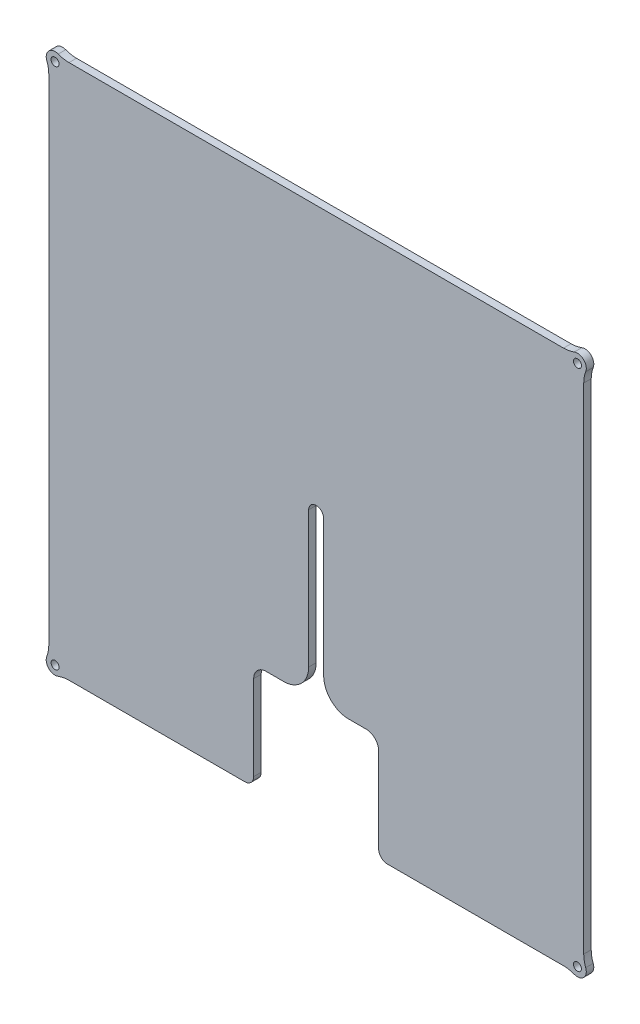
SolidWorks part; units mm, degrees
material "Balsa"
ref_plane "Front Plane" through (0, 0, 0) normal (0, 0, 1) x (1, 0, 0)
ref_plane "Top Plane" through (0, 0, 0) normal (0, 1, 0) x (1, 0, 0)
ref_plane "Right Plane" through (0, 0, 0) normal (1, 0, 0) x (0, 0, -1)
sketch "Sketch1" plane through (0, 0, 0) normal (0, 0, 1) x (1, 0, 0)
  line L0 (-107, 98.923) -> (-107, -98.923)
  line L1 (98.923, 107) -> (-98.923, 107)
  line L2 (107, -98.923) -> (107, 98.923)
  line L3 (43, -107) -> (98.923, -107)
  line L4 (43, -107) -> (43, -101) construction
  line L5 (39, -97) -> (-39, -97) construction
  line L6 (-43, -101) -> (-43, -107) construction
  line L7 (-98.923, -107) -> (-43, -107)
  line L8 (-43, -107) -> (43, -107)
  line L9 (104.5, -104.5) -> (-104.5, -104.5) construction
  line L10 (104.5, -104.5) -> (104.5, 104.5) construction
  line L11 (104.5, 104.5) -> (-104.5, 104.5) construction
  line L12 (-104.5, -104.5) -> (-104.5, 104.5) construction
  line L13 (104.5, -104.5) -> (-104.5, 104.5) construction
  line L14 (104.5, 104.5) -> (-104.5, -104.5) construction
  circle A0 centre (-104.5, -104.5) radius 1.6
  circle A1 centre (-104.5, 104.5) radius 1.6
  circle A2 centre (104.5, 104.5) radius 1.6
  circle A3 centre (104.5, -104.5) radius 1.6
  arc A4 (43, -101) -> (39, -97) centre (39, -101) ccw construction
  arc A5 (-39, -97) -> (-43, -101) centre (-39, -101) ccw construction
  arc A6 (-103.2308, 107.7999) -> (-107.7999, 103.2308) centre (-104.5, 104.5) ccw
  arc A8 (-107.7999, -103.2308) -> (-103.2308, -107.7999) centre (-104.5, -104.5) ccw
  arc A9 (98.923, -107) -> (103.2308, -107.7999) centre (98.923, -119) cw
  arc A10 (103.2308, -107.7999) -> (107.7999, -103.2308) centre (104.5, -104.5) ccw
  arc A13 (107.7999, 103.2308) -> (103.2308, 107.7999) centre (104.5, 104.5) ccw
  arc A14 (107, -98.923) -> (107.7999, -103.2308) centre (119, -98.923) ccw
  arc A15 (-103.2308, -107.7999) -> (-98.923, -107) centre (-98.923, -119) cw
  arc A16 (-107, -98.923) -> (-107.7999, -103.2308) centre (-119, -98.923) cw
  arc A17 (-107.7999, 103.2308) -> (-107, 98.923) centre (-119, 98.923) cw
  arc A18 (-103.2308, 107.7999) -> (-98.923, 107) centre (-98.923, 119) ccw
  arc A19 (107, 98.923) -> (107.7999, 103.2308) centre (119, 98.923) cw
  arc A20 (103.2308, 107.7999) -> (98.923, 107) centre (98.923, 119) cw
  point P0 (0, 0)
  dimension "D1" = 12
  dimension "D3" = 12
  dimension "D4" = 12
  dimension "D5" = 12
  dimension "D6" = 12
  dimension "D7" = 12
  dimension "D2" = 209
  dimension "D8" = 214
  dimension "D9" = 10
extrude "Boss-Extrude1" add sketch "Sketch1" along normal blind 3
sketch "Sketch3" plane through (0, 0, 3) normal (0, 0, 1) x (1, 0, 0)
  line L0 (-107, 98.923) -> (-107, -98.923) construction
  line L1 (71, -65) -> (-71, -65) construction
  line L2 (71, -65) -> (71, 65) construction
  line L3 (71, 65) -> (-71, 65) construction
  line L4 (-71, -65) -> (-71, 65) construction
  line L5 (71, -65) -> (-71, 65) construction
  line L6 (71, 65) -> (-71, -65) construction
  circle A0 centre (-71, 65) radius 1.6
  circle A1 centre (71, 65) radius 1.6
  circle A2 centre (71, -65) radius 1.6
  circle A3 centre (-71, -65) radius 1.6
  point P0 (0, 0)
  dimension "D3" = 3.2
  dimension "D1" = 36
  dimension "D2" = 130
extrude "Cut-Extrude2" [suppressed] cut sketch "Sketch3" against normal through all
sketch "Sketch5" plane through (0, 0, 0) normal (0, 0, 1) x (1, 0, 0)
  line L0 (-107, 0) -> (107, 0) construction
  line L1 (-107, 98.923) -> (-107, -98.923) construction
  line L2 (107, -98.923) -> (107, 98.923) construction
  line L3 (-98.923, -107) -> (98.923, -107) construction
  line L4 (-25.0334, -107) -> (24.9666, -107)
  line L12 (2.9666, 0) -> (2.9666, -54.5)
  line L13 (-3.0334, 0) -> (-3.0334, -54.5)
  line L14 (-13.0334, -64.5) -> (-20.0334, -64.5)
  line L15 (-25.0334, -69.5) -> (-25.0334, -107)
  line L16 (19.9666, -112) -> (-20.0334, -112) construction
  line L17 (24.9666, -69.5) -> (24.9666, -107)
  line L18 (19.9666, -64.5) -> (12.9666, -64.5)
  line L19 (-0.0334, 0) -> (-0.0334, -112) construction
  arc A15 (2.9666, -54.5) -> (12.9666, -64.5) centre (12.9666, -54.5) ccw
  arc A16 (2.9666, 0) -> (-3.0334, 0) centre (-0.0334, 0) ccw
  arc A17 (-13.0334, -64.5) -> (-3.0334, -54.5) centre (-13.0334, -54.5) ccw
  arc A18 (-20.0334, -64.5) -> (-25.0334, -69.5) centre (-20.0334, -69.5) ccw
  arc A19 (-25.0334, -107) -> (-20.0334, -112) centre (-20.0334, -107) ccw construction
  arc A20 (19.9666, -112) -> (24.9666, -107) centre (19.9666, -107) ccw construction
  arc A21 (24.9666, -69.5) -> (19.9666, -64.5) centre (19.9666, -69.5) ccw
  dimension "D5" = 10
  dimension "D6" = 5
  dimension "D1" = 50
  dimension "D2" = 64.5
extrude "Cut-Extrude5" cut sketch "Sketch5" along normal through all
sketch "Sketch4" [suppressed] plane through (0, 0, 3) normal (0, 0, 1) x (1, 0, 0)
  line L0 (-17, -97) -> (17, -97)
  line L1 (-39, -97) -> (-6, -97) construction
  line L2 (6, -97) -> (39, -97) construction
  line L3 (17, -97) -> (6, -83)
  line L4 (6, 0) -> (6, -97) construction
  line L5 (6, -83) -> (-6, -83)
  line L6 (-6, -97) -> (-6, 0) construction
  line L7 (-6, -83) -> (-17, -97)
  line L8 (-43, -107) -> (-43, -101) construction
  dimension "D1" = 26
  dimension "D2" = 14
extrude "Cut-Extrude3" [suppressed] cut sketch "Sketch4" against normal through all
fillet "Fillet1" radius 3.54 2 edges at (-25.0334, -107, 1.5) (24.9666, -107, 1.5)
